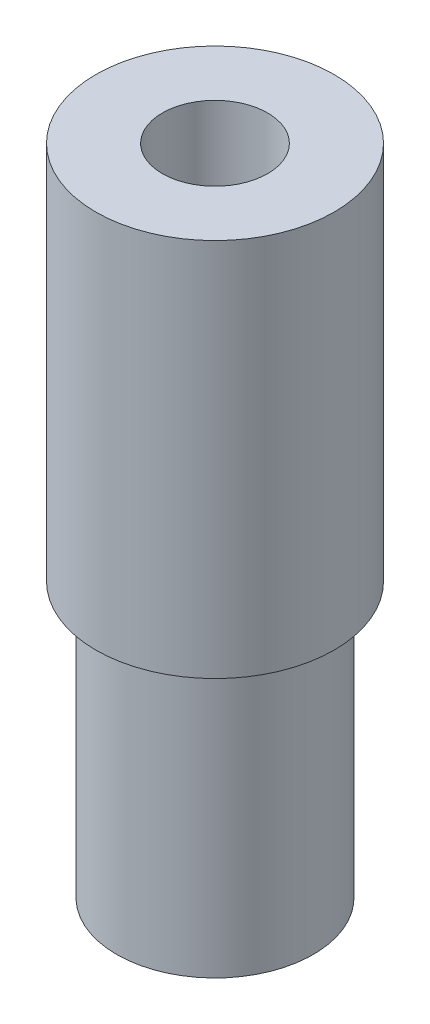
SolidWorks part; units mm, degrees
ref_plane "Front Plane" through (0, 0, 0) normal (0, 0, 1) x (1, 0, 0)
ref_plane "Top Plane" through (0, 0, 0) normal (0, 1, 0) x (1, 0, 0)
ref_plane "Right Plane" through (0, 0, 0) normal (1, 0, 0) x (0, 0, -1)
sketch "Sketch1" plane through (0, 0, 0) normal (0, 1, 0) x (1, 0, 0)
  circle A0 centre (0, 0) radius 4.95
  dimension "D1" = 9.9
extrude "Boss-Extrude1" add sketch "Sketch1" along normal blind 13.8
sketch "Sketch2" plane through (0, 13.8, 0) normal (0, 1, 0) x (1, 0, 0)
  circle A0 centre (0, 0) radius 6
  dimension "D1" = 12
extrude "Boss-Extrude2" add sketch "Sketch2" along normal blind 19.1
sketch "Sketch7" plane through (0, 0, 0) normal (0, 1, 0) x (1, 0, 0)
  circle A0 centre (0, 0) radius 2.65
  dimension "D1" = 5.3
extrude "Cut-Extrude1" cut sketch "Sketch7" along normal through all
chamfer "Chamfer1" distance 0.4 angle 45 1 edges at (0, 0, 2.65)
